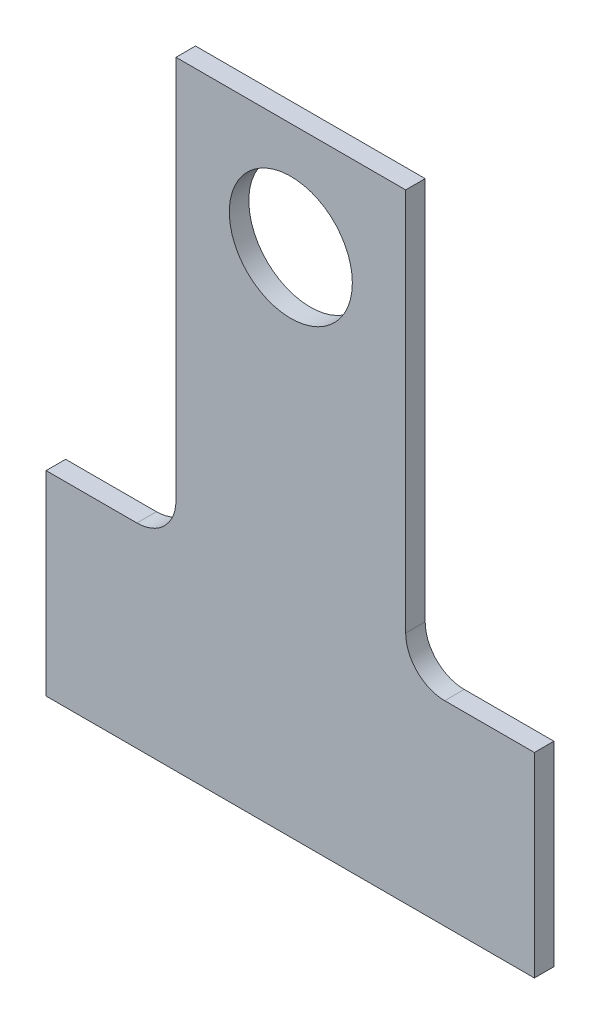
SolidWorks part; units mm, degrees
material "Nikiel"
ref_plane "Płaszczyzna przednia" through (0, 0, 0) normal (0, 0, 1) x (1, 0, 0)
ref_plane "Płaszczyzna górna" through (0, 0, 0) normal (0, 1, 0) x (1, 0, 0)
ref_plane "Płaszczyzna prawa" through (0, 0, 0) normal (1, 0, 0) x (0, 0, -1)
sketch "Szkic1" plane through (0, 0, 0) normal (0, 0, 1) x (1, 0, 0)
  line L6 (-12.5, -6) -> (-12.5, -16)
  line L10 (-12.5, -16) -> (12.5, -16)
  line L11 (12.5, -16) -> (12.5, -6)
  line L12 (7.91, -6) -> (12.5, -6)
  line L13 (-7.85, -6) -> (-12.5, -6)
  line L27 (-5.85, 15.65) -> (5.91, 15.65)
  line L29 (-5.85, -4) -> (-5.85, 15.65)
  line L30 (5.91, -4) -> (5.91, 15.65)
  arc A0 (-5.85, -4) -> (-7.85, -6) centre (-7.85, -4) cw
  arc A5 (5.91, -4) -> (7.91, -6) centre (7.91, -4) ccw
  point P0 (0, 0)
  dimension "D1" = 2
  dimension "D2" = 25
  dimension "D3" = 10
extrude "Dodanie-wyciągnięcie1" add sketch "Szkic1" along normal blind 1
sketch "Szkic2" plane through (0, 0, 1) normal (0, 0, 1) x (1, 0, 0)
  circle A15 centre (0.03, 10.16) radius 3.15
extrude "Wytnij-wyciągnięcie1" cut sketch "Szkic2" against normal blind 1
